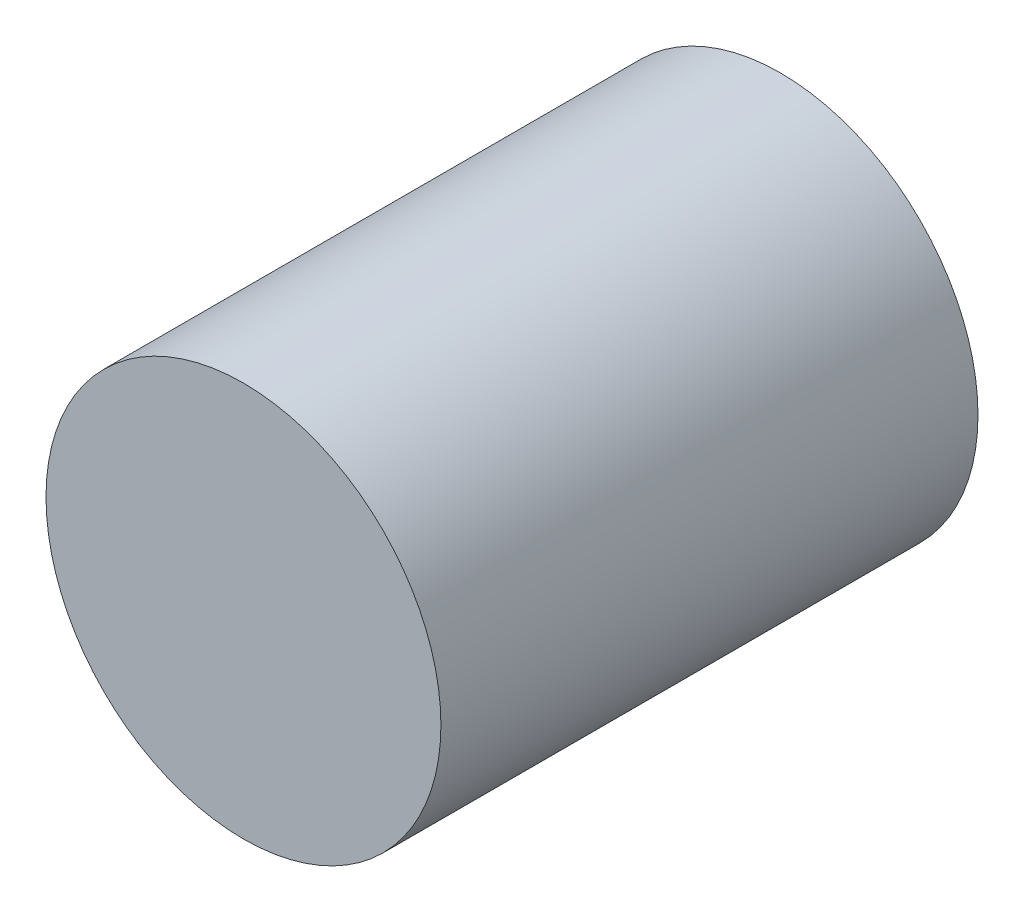
SolidWorks part; units mm, degrees
material "6061 Alloy"
ref_plane "Front Plane" through (0, 0, 0) normal (0, 0, 1) x (1, 0, 0)
ref_plane "Top Plane" through (0, 0, 0) normal (0, 1, 0) x (1, 0, 0)
ref_plane "Right Plane" through (0, 0, 0) normal (1, 0, 0) x (0, 0, -1)
sketch "Sketch1" plane through (0, 0, 0) normal (0, 0, 1) x (1, 0, 0)
  circle A0 centre (0, 0) radius 12.5
  dimension "D1" = 25
extrude "base" add sketch "Sketch1" along normal blind 34
